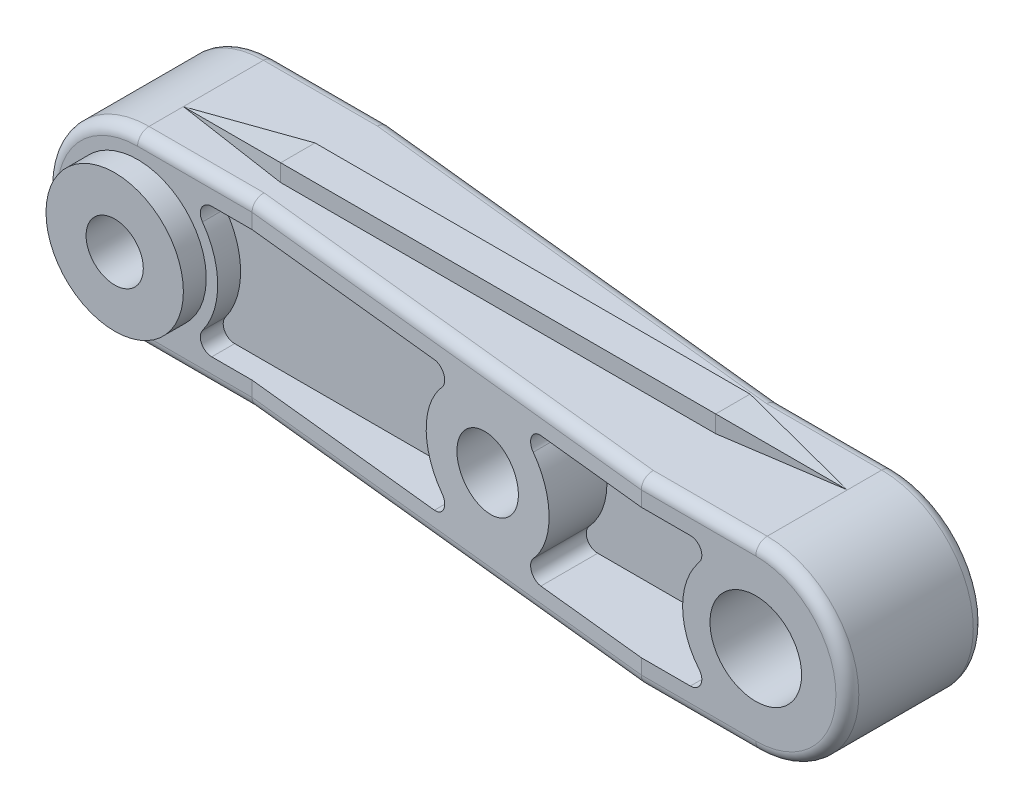
SolidWorks part; units mm, degrees
ref_plane "Plane1" through (0, 0, 0) normal (0, 0, 1) x (1, 0, 0)
ref_plane "Plane2" through (0, 0, 0) normal (0, 1, 0) x (1, 0, 0)
ref_plane "Plane3" through (0, 0, 0) normal (1, 0, 0) x (0, 0, -1)
sketch "Esquisse1" plane through (0, 0, 0) normal (0, 0, 1) x (1, 0, 0)
  line L0 (0, 0) -> (29, 0) construction
  line L1 (0, 4) -> (29, 4)
  line L2 (29, -4) -> (0, -4)
  arc A0 (0, 4) -> (0, -4) centre (0, 0) ccw
  arc A1 (29, -4) -> (29, 4) centre (29, 0) ccw
  circle A2 centre (29, 0) radius 2
  circle A3 centre (16.5, 0) radius 1.5
  dimension "D2" = 8
  dimension "D3" = 8
  dimension "D4" = 4
  dimension "D5" = 3
  dimension "D1" = 29
  dimension "D6" = 12.5
extrude "Base-Extrusion" add sketch "Esquisse1" along normal blind 8
sketch "Esquisse2" plane through (0, 0, 0) normal (0, 1, 0) x (1, 0, 0)
  line L0 (-4, 0) -> (5, 0)
  line L1 (0, 0) -> (-4, 0) construction
  line L2 (29, 0) -> (0, 0) construction
  line L3 (5, 0) -> (24, -2)
  line L4 (24, -2) -> (32, -2)
  line L5 (32, -2) -> (34, -2)
  line L6 (34, -2) -> (34, 2)
  line L7 (34, 2) -> (-5, 2)
  line L8 (-5, 2) -> (-5, 0)
  line L9 (-5, 0) -> (-4, 0)
  line L10 (30, -8) -> (24, -8)
  line L11 (29, -8) -> (33, -8) construction
  line L12 (29, -8) -> (0, -8) construction
  line L13 (24, -8) -> (5, -6)
  line L14 (5, -6) -> (-5, -6)
  line L15 (-5, -6) -> (-5, -9)
  line L16 (-5, -9) -> (35, -9)
  line L17 (35, -9) -> (35, -8)
  line L18 (35, -8) -> (30, -8)
  line L19 (29, -8) -> (29, 0) construction
  dimension "D1" = 9
  dimension "D2" = 19
  dimension "D3" = 5
  dimension "D4" = 6
  dimension "D5" = 6
  dimension "D6" = 19
extrude "Enlèv. mat.-Extru.1" cut sketch "Esquisse2" against normal mid plane 48
sketch "Esquisse3" plane through (0, 0, 8) normal (0, 0, 1) x (1, 0, 0)
  line L0 (29, 0) -> (0, 0) construction
  line L1 (26.1434, 2.846) -> (19.0974, 2.846)
  line L2 (26.1434, -2.846) -> (19.0974, -2.846)
  line L3 (13.9026, 2.846) -> (3.2398, 2.846)
  line L4 (13.9026, -2.846) -> (3.2398, -2.846)
  arc A0 (26.5298, 2.0287) -> (26.5298, -2.0287) centre (29, 0) ccw
  arc A1 (14.2737, 2.0109) -> (14.2737, -2.0109) centre (16.5, 0) ccw
  arc A2 (2.8348, -2.0528) -> (2.8348, 2.0528) centre (0, 0) ccw
  arc A3 (18.7263, -2.0109) -> (18.7263, 2.0109) centre (16.5, 0) ccw
  arc A4 (26.5298, 2.0287) -> (26.1434, 2.846) centre (26.1434, 2.346) ccw
  arc A5 (26.1434, -2.846) -> (26.5298, -2.0287) centre (26.1434, -2.346) ccw
  arc A6 (18.7263, -2.0109) -> (19.0974, -2.846) centre (19.0974, -2.346) ccw
  arc A7 (19.0974, 2.846) -> (18.7263, 2.0109) centre (19.0974, 2.346) ccw
  arc A8 (13.9026, 2.846) -> (14.2737, 2.0109) centre (13.9026, 2.346) cw
  arc A9 (13.9026, -2.846) -> (14.2737, -2.0109) centre (13.9026, -2.346) ccw
  arc A10 (2.8348, -2.0528) -> (3.2398, -2.846) centre (3.2398, -2.346) ccw
  arc A11 (3.2398, 2.846) -> (2.8348, 2.0528) centre (3.2398, 2.346) ccw
  point P7 (27.5448, 2.846)
  point P19 (27.5448, -2.846)
  point P22 (17.4488, -2.846)
  point P25 (17.4488, 2.846)
  point P28 (15.5512, 2.846)
  point P31 (15.5512, -2.846)
  point P34 (2.0372, -2.846)
  point P37 (2.0372, 2.846)
  dimension "D1" = 6
  dimension "D2" = 7
  dimension "D3" = 0.5
extrude "Enlèv. mat.-Extru.2" cut sketch "Esquisse3" against normal blind 3
ref_plane "Plan1" through (0, 0, 4) normal (0, 0, -1) x (-1, 0, 0)
mirror "Symétrie1" about plane through (0, 0, 4) normal (0, 0, -1)
sketch "Esquisse7" plane through (0, -4, 0) normal (0, -1, 0) x (1, 0, 0)
  line L0 (28, 4) -> (-7, 4) construction
  line L1 (33, 8) -> (29, 8) construction
  line L2 (5, 3.25) -> (24, 3.25)
  line L3 (5, 4.75) -> (24, 4.75)
  line L4 (24, 3.25) -> (29, 4)
  line L5 (24, 4.75) -> (29, 4)
  line L6 (5, 3.25) -> (0, 4)
  line L7 (5, 4.75) -> (0, 4)
  dimension "D1" = 4
  dimension "D2" = 1.5
  dimension "D3" = 19
  dimension "D4" = 5
  dimension "D5" = 5
extrude "Boss.-Extru.2" add sketch "Esquisse7" along normal blind 0.75
mirror "Symétrie2" about plane through (0, 0, 0) normal (0, 1, 0)
sketch "Esquisse8" plane through (0, 0, 4.75) normal (0, 0, 1) x (1, 0, 0)
  line L0 (0, 4) -> (5, 4.75)
  line L1 (5, 4.75) -> (5, 7)
  line L2 (5, 7) -> (0, 7)
  line L3 (0, 7) -> (0, 4)
  line L4 (24, 4.75) -> (29, 4)
  line L5 (29, 4) -> (29, 7)
  line L6 (29, 7) -> (24, 7)
  line L7 (24, 7) -> (24, 4.75)
  line L8 (0, 0) -> (29, 0) construction
  line L9 (29, -7) -> (24, -7)
  line L10 (29, -4) -> (29, -7)
  line L11 (24, -4.75) -> (29, -4)
  line L12 (24, -7) -> (24, -4.75)
  line L13 (5, -4.75) -> (5, -7)
  line L14 (5, -7) -> (0, -7)
  line L15 (0, -7) -> (0, -4)
  line L16 (0, -4) -> (5, -4.75)
extrude "Enlèv. mat.-Extru.3" cut sketch "Esquisse8" against normal through all
fillet "Congé1" radius 0.5
sketch "Esquisse9" plane through (0, 0, 6) normal (0, 0, 1) x (1, 0, 0)
  circle A0 centre (0, 0) radius 3
  dimension "D1" = 6
extrude "Boss.-Extru.3" add sketch "Esquisse9" along normal blind 1
sketch "Esquisse10" plane through (0, 0, 7) normal (0, 0, 1) x (1, 0, 0)
  circle A0 centre (0, 0) radius 1.25
  dimension "D1" = 2.5
extrude "Enlèv. mat.-Extru.4" cut sketch "Esquisse10" against normal through all
